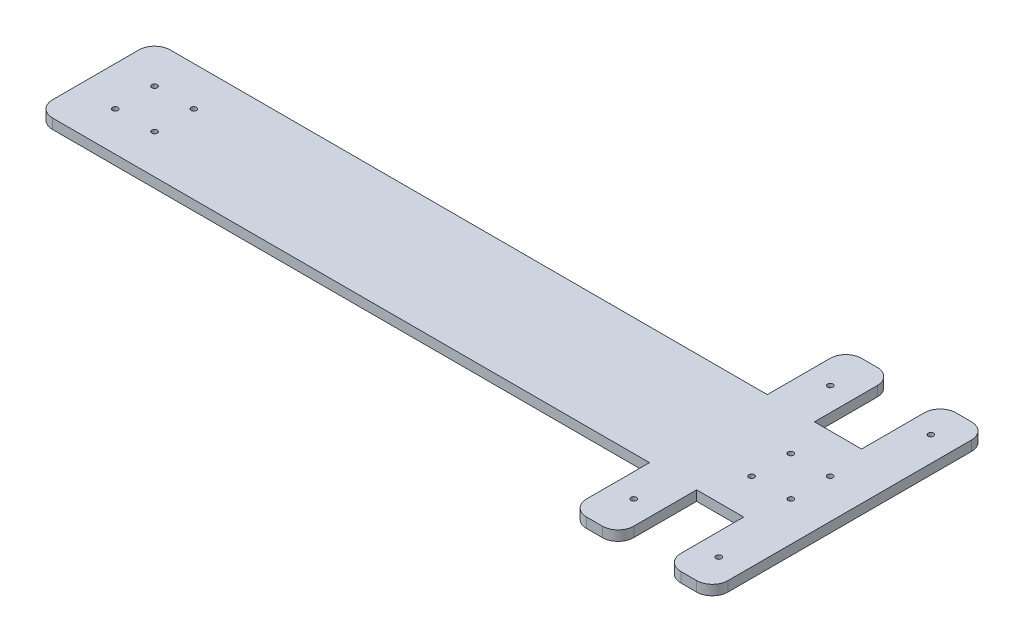
SolidWorks part; units mm, degrees
ref_plane "Front Plane" through (0, 0, 0) normal (0, 0, 1) x (1, 0, 0)
ref_plane "Top Plane" through (0, 0, 0) normal (0, 1, 0) x (1, 0, 0)
ref_plane "Right Plane" through (0, 0, 0) normal (1, 0, 0) x (0, 0, -1)
sketch "Sketch1" plane through (0, 0, 0) normal (0, 1, 0) x (1, 0, 0)
  line L0 (-240, 37.5) -> (150, 37.5)
  line L1 (150, 37.5) -> (150, 87.5)
  line L2 (150, 87.5) -> (180, 87.5)
  line L3 (180, 87.5) -> (180, 37.5)
  line L4 (180, 37.5) -> (210, 37.5)
  line L5 (210, 37.5) -> (210, 87.5)
  line L6 (210, 87.5) -> (240, 87.5)
  line L7 (240, 87.5) -> (240, -87.5)
  line L8 (240, -87.5) -> (210, -87.5)
  line L9 (210, -87.5) -> (210, -37.5)
  line L10 (210, -37.5) -> (180, -37.5)
  line L11 (180, -37.5) -> (180, -87.5)
  line L12 (180, -87.5) -> (150, -87.5)
  line L13 (150, -87.5) -> (150, -37.5)
  line L14 (150, -37.5) -> (-240, -37.5)
  line L15 (-240, -37.5) -> (-240, 37.5)
  line L16 (-240, 0) -> (240, 0) construction
  point P18 (0, 0)
  dimension "D1" = 75
  dimension "D2" = 30
  dimension "D3" = 30
  dimension "D4" = 480
  dimension "D5" = 50
extrude "Boss-Extrude2" add sketch "Sketch1" along normal blind 6.35
sketch "Sketch2" plane through (0, 6.35, 0) normal (0, 1, 0) x (1, 0, 0)
  line L0 (240, 87.5) -> (210, 87.5) construction
  line L1 (240, -87.5) -> (240, 87.5) construction
  circle A0 centre (190, 12.5) radius 1.75
  dimension "D1" = 75
  dimension "D3" = 3.5
  dimension "D2" = 50
extrude "Cut-Extrude1" cut sketch "Sketch2" against normal blind 6.35
pattern_linear "LPattern1" count 2 spacing 25 along (1, 0, 0) of "Cut-Extrude1"
pattern_linear "LPattern2" count 2 spacing 25 along (0, 0, 1) of "LPattern1", "Cut-Extrude1"
fillet "Fillet1" radius 10 10 edges at (150, 3.175, -87.5) (180, 3.175, -87.5) (210, 3.175, -87.5) (240, 3.175, -87.5) (240, 3.175, 87.5) (210, 3.175, 87.5) (180, 3.175, 87.5) (150, 3.175, 87.5) (-240, 3.175, 37.5) (-240, 3.175, -37.5)
sketch "Sketch3" plane through (0, 6.35, 0) normal (0, 1, 0) x (1, 0, 0)
  line L0 (240, -77.5) -> (240, 77.5) construction
  line L1 (230, 87.5) -> (220, 87.5) construction
  line L2 (220, -87.5) -> (230, -87.5) construction
  circle A0 centre (224.12, 67.5) radius 1.75
  circle A1 centre (224.12, -67.5) radius 1.75
  dimension "D1" = 3.5
  dimension "D4" = 3.5
  dimension "D2" = 15.88
  dimension "D3" = 20
  dimension "D5" = 20
  dimension "D6" = 15.88
extrude "Cut-Extrude2" cut sketch "Sketch3" against normal through all
sketch "Sketch5" plane through (0, 6.35, 0) normal (0, 1, 0) x (1, 0, 0)
  line L0 (170, 87.5) -> (160, 87.5) construction
  line L3 (160, -87.5) -> (170, -87.5) construction
  line L4 (240, -77.5) -> (240, 77.5) construction
  circle A0 centre (165, 62.5) radius 1.75
  circle A1 centre (165, -62.5) radius 1.75
  dimension "D1" = 25
  dimension "D3" = 3.5
  dimension "D4" = 3.5
  dimension "D2" = 75
  dimension "D5" = 75
  dimension "D6" = 25
extrude "Cut-Extrude3" cut sketch "Sketch5" against normal through all
pattern_linear "LPattern3" count 2 spacing 405 along (-1, 0, 0) of "LPattern2", "LPattern1", "Cut-Extrude1"
